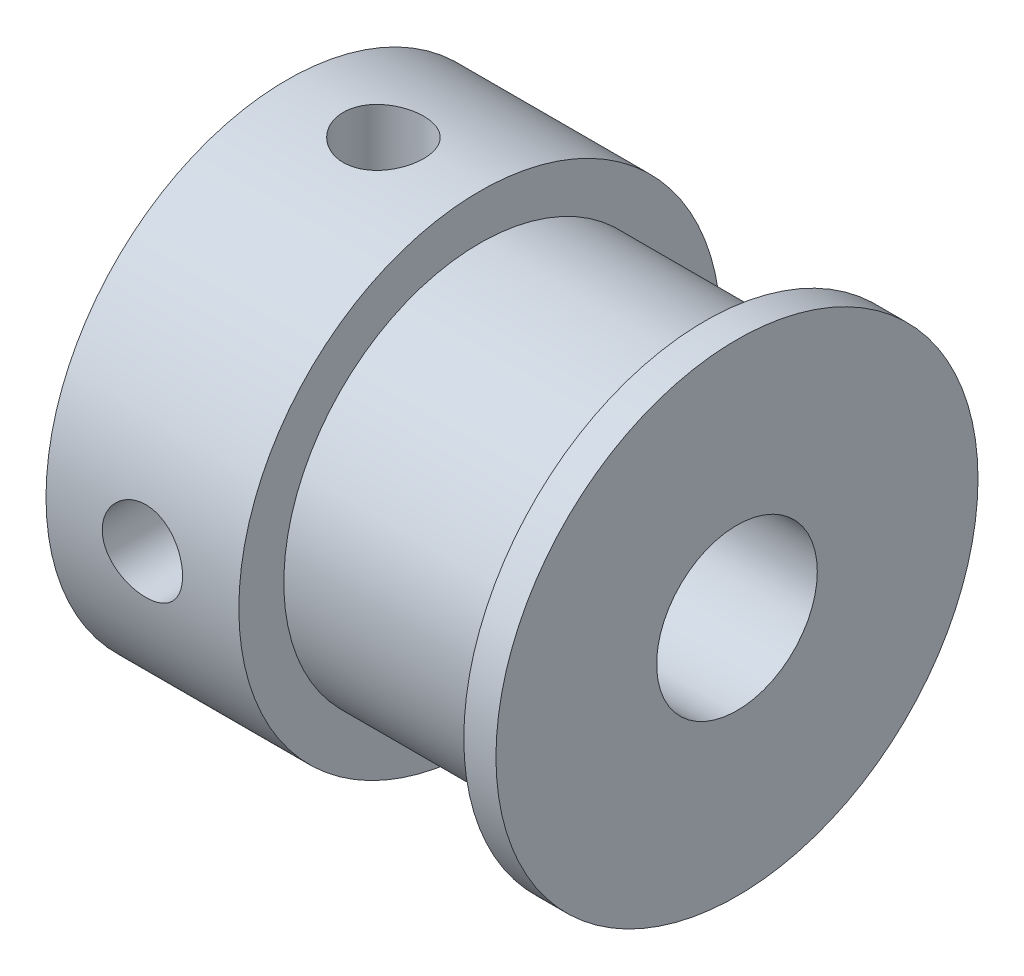
SolidWorks part; units mm, degrees
material "6061-T6 (SS)"
ref_plane "Front Plane" through (0, 0, 0) normal (0, 0, 1) x (1, 0, 0)
ref_plane "Top Plane" through (0, 0, 0) normal (0, 1, 0) x (1, 0, 0)
ref_plane "Right Plane" through (0, 0, 0) normal (1, 0, 0) x (0, 0, -1)
sketch "Sketch1" plane through (0, 0, 0) normal (0, 0, 1) x (1, 0, 0)
  line L0 (0, 2.5) -> (0, 7.5)
  line L1 (0, 7.5) -> (6, 7.5)
  line L2 (6, 7.5) -> (6, 6.1)
  line L3 (6, 6.1) -> (13, 6.1)
  line L4 (13, 6.1) -> (13, 7.5)
  line L5 (13, 7.5) -> (14, 7.5)
  line L6 (14, 7.5) -> (14, 2.5)
  line L7 (14, 2.5) -> (0, 2.5)
  line L8 (0, 0) -> (-7.6744, 0) construction
  dimension "D1" = 5
  dimension "D2" = 15
  dimension "D3" = 12.2
  dimension "D4" = 6
  dimension "D5" = 14
  dimension "D6" = 1
revolve "Revolve1" add sketch "Sketch1" angle 360 about L8
hole_wizard "M3x0.5 Tapped Hole1" positions "Sketch3" profile "Sketch2" tap size "M3x0.5" standard "ANSI Metric"
sketch "Sketch3" plane through (0, 0, 0) normal (0, 1, 0) x (1, 0, 0)
  line L0 (0, 0) -> (6, 0) construction
  line L1 (6, -6.1) -> (6, 6.1) construction
  point P8 (3, 0)
sketch "Sketch2" plane through (3, 0, 0) normal (1, 0, 0) x (0, 0, -1)
  line L0 (0, 0) -> (0, 7.5)
  line L1 (0, 7.5) -> (1.25, 7.5)
  line L2 (1.25, 7.5) -> (1.25, 0)
  line L5 (1.25, 0) -> (0, 0)
  line L11 (0, -6.35) -> (0, 107.95) construction
  dimension "Thread Major Dia." = 2.5
  dimension "Thru Tap Drill Depth" = 7.5
hole_wizard "M3x0.5 Tapped Hole2" positions "Sketch5" profile "Sketch4" tap size "M3x0.5" standard "ANSI Metric"
sketch "Sketch5" plane through (0, 0, 0) normal (0, 0, 1) x (1, 0, 0)
  line L0 (0, 0) -> (6, 0) construction
  line L1 (6, -6.1) -> (6, 6.1) construction
  point P7 (3, 0)
sketch "Sketch4" plane through (3, 0, 0) normal (1, 0, 0) x (0, 1, 0)
  line L0 (0, 0) -> (0, 7.5)
  line L1 (0, 7.5) -> (1.25, 7.5)
  line L2 (1.25, 7.5) -> (1.25, 0)
  line L5 (1.25, 0) -> (0, 0)
  line L11 (0, -6.35) -> (0, 107.95) construction
  dimension "Thread Major Dia." = 2.5
  dimension "Thru Tap Drill Depth" = 7.5
